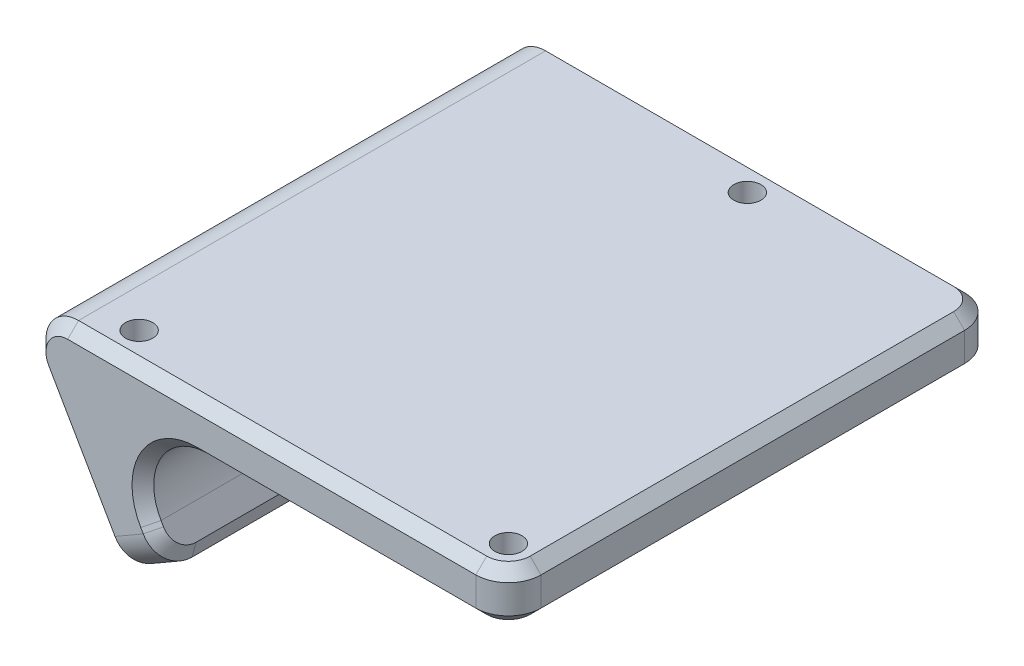
SolidWorks part; units mm, degrees
material "6061 合金"
ref_plane "前视基准面" through (0, 0, 0) normal (0, 0, 1) x (1, 0, 0)
ref_plane "上视基准面" through (0, 0, 0) normal (0, 1, 0) x (1, 0, 0)
ref_plane "右视基准面" through (0, 0, 0) normal (1, 0, 0) x (0, 0, -1)
sketch "草图1" plane through (0, 0, 0) normal (0, 0, 1) x (1, 0, 0)
  line L0 (40, 0) -> (-5.7735, 0)
  line L1 (-100019.6299, 173229.0808) -> (100036.2838, -173277.9261) construction
  line L2 (40, 0) -> (40, -4.6509)
  line L4 (173304.7549, 100029.802) -> (-173180.2682, -100013.4194) construction
  line L5 (40, -4.6509) -> (2.6852, -4.6509)
  line L6 (-3.0883, -4.6509) -> (4.4117, -17.6412) construction
  line L7 (-5.7735, 0) -> (4.4117, -17.6412)
  line L8 (4.4117, -17.6412) -> (8.7418, -15.1412)
  line L9 (-100015.2998, 173231.5808) -> (100040.6139, -173275.4261) construction
  line L10 (8.7418, -15.1412) -> (2.6852, -4.6509)
extrude "凸台-拉伸1" add sketch "草图1" against normal up to surface (45 mm away)
fillet "圆角1" radius 3 2 edges at (40, -2.3254, 0) (40, -2.3254, -45)
fillet "圆角2" radius 5 1 edges at (2.6852, -4.6509, -22.5)
fillet "圆角3" radius 3 1 edges at (-5.7735, 0, -22.5)
fillet "圆角4" radius 3 2 edges at (6.5767, -16.3912, -45) (6.5767, -16.3912, 0)
chamfer "倒角1" distance 1 angle 45 12 edges at (7.0153, -7.1509, -45) (7.1286, -12.347, -45) (24.1727, -4.6509, -45) (8.3025, -14.3803, -44.1213) (39.1213, -4.6509, -44.1213) (8.7418, -15.1412, -22.5) (40, -4.6509, -22.5) (8.3025, -14.3803, -0.8787) (39.1213, -4.6509, -0.8787) (7.1286, -12.347, 0) (24.1727, -4.6509, 0) (7.0153, -7.1509, 0)
sketch "草图2" plane through (0, 0, 0) normal (0, 1, 0) x (1, 0, 0)
  point P0 (20, 42)
  point P1 (3, 3)
  point P3 (37, 3)
hole_wizard "M3 螺纹孔1" positions "草图3" profile "草图4" tap size "M3" standard "GB"
sketch "草图3" plane through (0, 0, 0) normal (0, 1, 0) x (1, 0, 0)
  point P0 (20, 42)
  point P3 (3, 3)
  point P6 (37, 3)
sketch "草图4" plane through (20, 0, -42) normal (1, 0, 0) x (0, 0, 1)
  line L0 (0, 0) -> (0, 8.2511)
  line L1 (0, 8.2511) -> (1.25, 7.5)
  line L2 (1.25, 7.5) -> (1.25, 0)
  line L5 (1.25, 0) -> (0, 0)
  line L10 (0, 8.2511) -> (-1.25, 7.5) construction
  line L11 (0, -6.35) -> (0, 107.95) construction
  dimension "螺纹孔钻头直径" = 2.5
  dimension "螺纹孔钻头深度" = 7.5
  dimension "导头角度" = 118
cosmetic thread "孔螺蚊线1" parameters "D1"=6, "D2"=3
cosmetic thread "孔螺蚊线2" parameters "D1"=6, "D2"=3
cosmetic thread "孔螺蚊线3" parameters "D1"=6, "D2"=3
chamfer "倒角2" distance 1 angle 45 12 edges at (-3.1754, -1.5, -45) (18.2113, 0, -45) (-0.1319, -9.7716, -45) (39.1213, 0, -44.1213) (3.9723, -16.8803, -44.1213) (40, 0, -22.5) (4.4117, -17.6412, -22.5) (39.1213, 0, -0.8787) (3.9723, -16.8803, -0.8787) (18.2113, 0, 0) (-0.1319, -9.7716, 0) (-3.1754, -1.5, 0)
sketch "草图5" plane through (-4.3301, -2.5, 0) normal (-0.866, -0.5, 0) x (0, 0, 1)
  line L0 (-11.75, -8.3965) -> (-11.75, -4.3965) construction
  line L1 (-44, -2.3094) -> (-44, -14.4836) construction
  line L2 (-1, -14.4836) -> (-1, -2.3094) construction
  line L3 (-22.5, -8.3965) -> (-22.5, -12.3965) construction
  line L4 (-22.5, -106.5187) -> (-22.5, -55.9369) construction
  line L5 (-22.5, -8.3965) -> (-44, -8.3965) construction
  line L6 (-22.5, -8.3965) -> (-1, -8.3965) construction
  line L7 (-33.25, -8.3965) -> (-33.25, -4.3965) construction
  line L8 (-33.25, -4.3965) -> (-22.5, -12.3965) construction
  line L9 (-22.5, -12.3965) -> (-11.75, -4.3965) construction
  line L10 (-33.25, -8.3965) -> (-44, -8.3965) construction
  line L11 (-11.75, -8.3965) -> (-1, -8.3965) construction
  point P12 (-27.875, -8.3965)
  point P13 (-38.625, -8.3965)
  point P16 (-6.375, -8.3965)
  point P17 (-17.125, -8.3965)
  point P19 (-22.5, -8.3965)
hole_wizard "M3 螺纹孔2" positions "草图6" profile "草图7" tap size "M3" standard "GB"
sketch "草图6" plane through (-4.3301, -2.5, 0) normal (-0.866, -0.5, 0) x (0, 0, 1)
  point P0 (-38.625, -8.3965)
  point P3 (-33.25, -4.3965)
  point P6 (-27.875, -8.3965)
  point P9 (-22.5, -12.3965)
  point P12 (-17.125, -8.3965)
  point P15 (-11.75, -4.3965)
  point P18 (-6.375, -8.3965)
sketch "草图7" plane through (-0.1319, -9.7716, -38.625) normal (0, 0, 1) x (0.5, -0.866, 0)
  line L0 (0, 0) -> (0, 8.2511)
  line L1 (0, 8.2511) -> (1.25, 7.5)
  line L2 (1.25, 7.5) -> (1.25, 0)
  line L5 (1.25, 0) -> (0, 0)
  line L10 (0, 8.2511) -> (-1.25, 7.5) construction
  line L11 (0, -6.35) -> (0, 107.95) construction
  dimension "螺纹孔钻头直径" = 2.5
  dimension "螺纹孔钻头深度" = 7.5
  dimension "导头角度" = 118
cosmetic thread "孔螺蚊线4" parameters "D1"=6, "D2"=3
cosmetic thread "孔螺蚊线5" parameters "D1"=6, "D2"=3
cosmetic thread "孔螺蚊线6" parameters "D1"=6, "D2"=3
cosmetic thread "孔螺蚊线7" parameters "D1"=6, "D2"=3
cosmetic thread "孔螺蚊线8" parameters "D1"=6, "D2"=3
cosmetic thread "孔螺蚊线9" parameters "D1"=6, "D2"=3
cosmetic thread "孔螺蚊线10" parameters "D1"=6, "D2"=3
